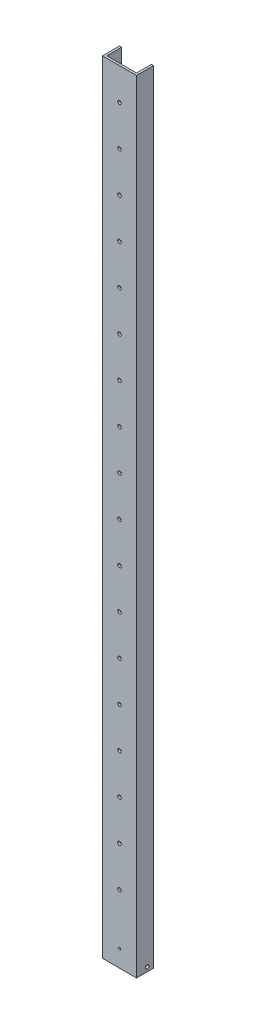
SolidWorks part; units mm, degrees
ref_plane "Front" through (0, 0, 0) normal (0, 0, 1) x (1, 0, 0)
ref_plane "Top" through (0, 0, 0) normal (0, 1, 0) x (1, 0, 0)
ref_plane "Right" through (0, 0, 0) normal (1, 0, 0) x (0, 0, -1)
sketch "Sketch1" plane through (0, 0, 0) normal (0, 1, 0) x (1, 0, 0)
  line L0 (3.175, 3.175) -> (3.175, 25.4)
  line L1 (0, 0) -> (50.8, 0)
  line L2 (0, 0) -> (0, 25.4)
  line L4 (50.8, 0) -> (50.8, 25.4)
  line L5 (3.175, 3.175) -> (47.625, 3.175)
  line L6 (47.625, 3.175) -> (47.625, 25.4)
  line L7 (0, 25.4) -> (3.175, 25.4)
  line L8 (50.8, 25.4) -> (47.625, 25.4)
  dimension "D1" = 25.4
  dimension "D2" = 50.8
  dimension "D3" = 3.175
extrude "Boss-Extrude1" add sketch "Sketch1" along normal blind 1168.4
sketch "Sketch2" plane through (0, 0, 0) normal (0, 0, 1) x (1, 0, 0)
  line L0 (25.4, 0) -> (25.4, 101.6) construction
  line L1 (0, 0) -> (50.8, 0) construction
  circle A0 centre (25.4, 101.6) radius 2.667
  circle A1 centre (25.4, 161.544) radius 2.667
  circle A2 centre (25.4, 221.488) radius 2.667
  circle A3 centre (25.4, 281.432) radius 2.667
  circle A4 centre (25.4, 341.376) radius 2.667
  circle A5 centre (25.4, 401.32) radius 2.667
  circle A6 centre (25.4, 461.264) radius 2.667
  circle A7 centre (25.4, 521.208) radius 2.667
  circle A8 centre (25.4, 581.152) radius 2.667
  circle A11 centre (25.4, 641.096) radius 2.667
  circle A12 centre (25.4, 701.04) radius 2.667
  circle A13 centre (25.4, 760.984) radius 2.667
  circle A14 centre (25.4, 820.928) radius 2.667
  circle A15 centre (25.4, 880.872) radius 2.667
  circle A16 centre (25.4, 940.816) radius 2.667
  circle A17 centre (25.4, 1000.76) radius 2.667
  circle A18 centre (25.4, 1060.704) radius 2.667
  circle A19 centre (25.4, 1120.648) radius 2.667
  dimension "D2" = 5.334
  dimension "D1" = 101.6
  dimension "D3" = 18
extrude "Igus_Holes" cut sketch "Sketch2" against normal up to next
sketch "Sketch3" plane through (0, 0, -3.175) normal (0, 0, -1) x (-1, 0, 0)
  line L0 (-25.4, 0) -> (-25.4, 25.4) construction
  line L1 (-47.625, 0) -> (-3.175, 0) construction
  circle A0 centre (-25.4, 25.4) radius 1.5875
  point P11 (0, 0)
  dimension "D2" = 3.175
  dimension "D1" = 25.4
extrude "Cut-Extrude2" cut sketch "Sketch3" against normal up to next
sketch "Sketch4" plane through (0, 0, 0) normal (-1, 0, 0) x (0, 0, 1)
  line L0 (-15.875, 0) -> (-15.875, 6.35) construction
  line L2 (-25.4, 0) -> (0, 0) construction
  line L3 (-15.875, 6.35) -> (-25.4, 6.35) construction
  line L4 (-25.4, 1168.4) -> (-25.4, 0) construction
  circle A0 centre (-15.875, 6.35) radius 2.667
  dimension "D2" = 5.334
  dimension "D1" = 6.35
  dimension "D3" = 9.525
extrude "Cut-Extrude3" cut sketch "Sketch4" against normal through all
ref_plane "Mid_Plane" through (25.4, 0, 0) normal (1, 0, 0) x (0, 0, -1)
